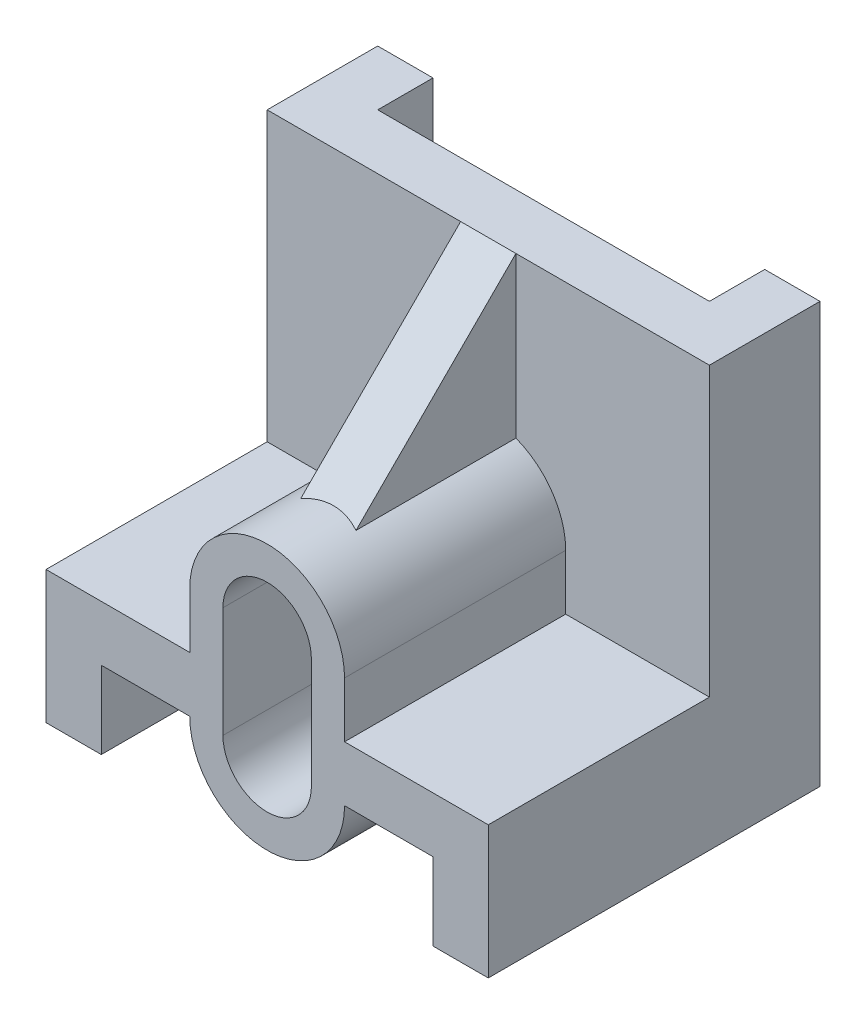
SolidWorks part; units mm, degrees
material "Alloy Steel"
ref_plane "Front Plane" through (0, 0, 0) normal (0, 0, 1) x (1, 0, 0)
ref_plane "Top Plane" through (0, 0, 0) normal (0, 1, 0) x (1, 0, 0)
ref_plane "Right Plane" through (0, 0, 0) normal (1, 0, 0) x (0, 0, -1)
sketch "Sketch1" plane through (0, 0, 0) normal (1, 0, 0) x (0, 0, -1)
  line L0 (0, 38) -> (0, 0)
  line L1 (0, 0) -> (-30, 0)
  line L2 (-30, 0) -> (-30, 12)
  line L3 (-30, 12) -> (-10, 12)
  line L4 (-10, 12) -> (-10, 38)
  line L5 (-10, 38) -> (0, 38)
  dimension "D1" = 30
  dimension "D2" = 38
  dimension "D3" = 12
  dimension "D4" = 10
extrude "Boss-Extrude1" add sketch "Sketch1" along normal mid plane 40
sketch "Sketch2" plane through (0, 0, 30) normal (0, 0, 1) x (1, 0, 0)
  line L0 (0, 0) -> (0, 32.0324) construction
  line L1 (20, 0) -> (-20, 0) construction
  line L2 (-15, 0) -> (15, 0)
  line L3 (-15, 0) -> (-15, 7)
  line L4 (-15, 7) -> (15, 7)
  line L5 (15, 0) -> (15, 7)
  dimension "D1" = 30
  dimension "D2" = 7
extrude "Cut-Extrude1" cut sketch "Sketch2" against normal through all
sketch "Sketch3" plane through (0, 0, 30) normal (0, 0, 1) x (1, 0, 0)
  line L0 (0, 17) -> (0, 7) construction
  line L1 (20, 12) -> (-20, 12) construction
  line L2 (7, 17) -> (7, 7)
  line L3 (-7, 17) -> (-7, 7)
  arc A0 (7, 17) -> (-7, 17) centre (0, 17) ccw
  arc A1 (-7, 7) -> (7, 7) centre (0, 7) ccw
  point P5 (0, 12)
  dimension "D2" = 7
  dimension "D1" = 10
extrude "Boss-Extrude3" add sketch "Sketch3" against normal up to surface (30 mm away) up to face at (0, 11.25, 0)
sketch "Sketch4" plane through (0, 0, 30) normal (0, 0, 1) x (1, 0, 0)
  line L0 (0, 17) -> (0, 7) construction
  line L1 (4, 17) -> (4, 7)
  line L2 (-4, 17) -> (-4, 7)
  arc A1 (4, 17) -> (-4, 17) centre (0, 17) ccw
  arc A2 (-4, 7) -> (4, 7) centre (0, 7) ccw
  point P0 (0, 12)
  dimension "D1" = 4
extrude "Cut-Extrude2" cut sketch "Sketch4" against normal through all
sketch "Sketch5" plane through (0, 38, 0) normal (0, 1, 0) x (1, 0, 0)
  line L0 (0, 0) -> (0, -19.9704) construction
  line L1 (20, 0) -> (-20, 0) construction
  line L2 (-15, 0) -> (15, 0)
  line L3 (-15, 0) -> (-15, -5)
  line L4 (-15, -5) -> (15, -5)
  line L5 (15, 0) -> (15, -5)
  dimension "D1" = 30
  dimension "D2" = 5
extrude "Cut-Extrude3" cut sketch "Sketch5" against normal through all
sketch "Sketch6" plane through (0, 0, 0) normal (1, 0, 0) x (0, 0, -1)
  line L0 (-10, 38) -> (-24, 24)
  line L1 (-10, 38) -> (-10, 12) construction
  dimension "D1" = 14
  dimension "D2" = 45
rib "Rib2" sketch "Sketch6" sketch "Sketch6" thickness 5 extrusion direction parallel to sketch draft on no parameters "D1"=5
